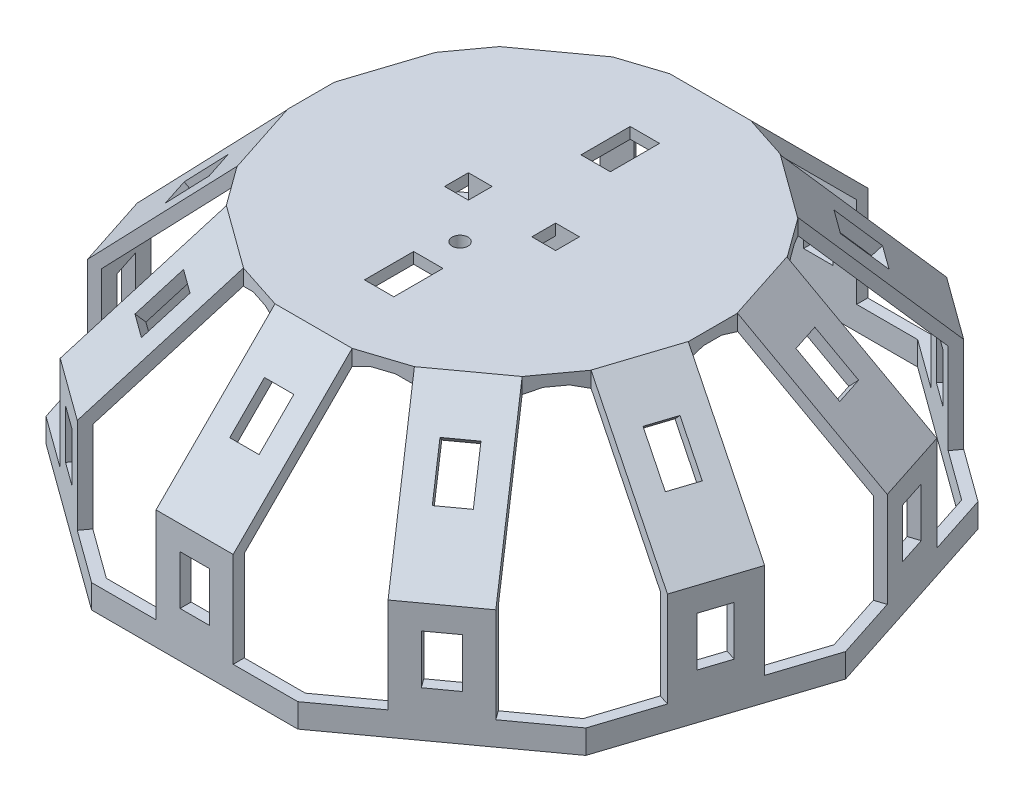
SolidWorks part; units mm, degrees
ref_plane "Front Plane" through (0, 0, 0) normal (0, 0, 1) x (1, 0, 0)
ref_plane "Top Plane" through (0, 0, 0) normal (0, 1, 0) x (1, 0, 0)
ref_plane "Right Plane" through (0, 0, 0) normal (1, 0, 0) x (0, 0, -1)
sketch "Sketch1" plane through (0, 0, 0) normal (0, 1, 0) x (1, 0, 0)
  line L0 (-34.026, -24.7214) -> (-12.9968, -40)
  line L1 (42.0585, 0) -> (34.026, 24.7214)
  line L2 (34.026, 24.7214) -> (12.9968, 40)
  line L3 (12.9968, 40) -> (-12.9968, 40)
  line L4 (-12.9968, 40) -> (-34.026, 24.7214)
  line L5 (-34.026, 24.7214) -> (-42.0585, 0)
  line L6 (-42.0585, 0) -> (-34.026, -24.7214)
  line L7 (-12.9968, -40) -> (12.9968, -40)
  line L8 (12.9968, -40) -> (34.026, -24.7214)
  line L9 (34.026, -24.7214) -> (42.0585, 0)
  circle A0 centre (0, 0) radius 40 construction
  point P14 (0, 40)
  dimension "D1" = 40
extrude "Boss-Extrude1" add sketch "Sketch1" along normal blind 30
chamfer "Chamfer1" distance 15 angle 45 10 edges at (23.5114, 30, 32.3607) (0, 30, 40) (-23.5114, 30, 32.3607) (-38.0423, 30, 12.3607) (-38.0423, 30, -12.3607) (-23.5114, 30, -32.3607) (0, 30, -40) (23.5114, 30, -32.3607) (38.0423, 30, -12.3607) (38.0423, 30, 12.3607)
ref_plane "Half Height Plane" through (0, 15, 0) normal (0, -1, 0) x (-1, 0, 0)
ref_plane "Sensor Reference Plane 1" through (0, 22.5, 0) normal (0, 1, 0) x (1, 0, 0)
ref_plane "Sensor Reference Plane 2" through (0, 7.5, 0) normal (0, -1, 0) x (-1, 0, 0)
ref_plane "Plane Angle 1" through (0, 0, 0) normal (-1, 0, 0) x (0, 0, 1)
ref_plane "Plane Angle 2" through (0, 0, 0) normal (0.809, 0, -0.5878) x (-0.5878, 0, -0.809)
ref_plane "Plane Angle 3" through (0, 0, 0) normal (0.309, 0, -0.9511) x (-0.9511, 0, -0.309)
ref_plane "Plane Angle 4" through (0, 0, 0) normal (-0.309, 0, -0.9511) x (-0.9511, 0, 0.309)
ref_plane "Plane Angle 5" through (0, 0, 0) normal (-0.809, 0, -0.5878) x (-0.5878, 0, 0.809)
sketch3d "3DSketch2"
  line L0 (-8.123, 30, 25) -> (8.123, 30, 25) construction
  line L1 (8.123, 30, -25) -> (-8.123, 30, -25) construction
  line L2 (0, 7.5, 40) -> (0, 7.5, 50)
  line L3 (38.0423, 7.5, 12.3607) -> (47.5528, 7.5, 15.4508)
  line L4 (0, 22.5, 32.5) -> (0, 29.5711, 39.5711)
  line L5 (23.5114, 7.5, 32.3607) -> (29.3893, 7.5, 40.4508)
  line L6 (19.103, 22.5, 26.2931) -> (23.2593, 29.5711, 32.0137)
  line L7 (30.9093, 22.5, 10.0431) -> (37.6343, 29.5711, 12.2281)
  line L8 (38.0423, 7.5, -12.3607) -> (47.5528, 7.5, -15.4508)
  line L9 (30.9093, 22.5, -10.0431) -> (37.6343, 29.5711, -12.2281)
  line L10 (23.5114, 7.5, -32.3607) -> (29.3893, 7.5, -40.4508)
  line L11 (19.103, 22.5, -26.2931) -> (23.2593, 29.5711, -32.0137)
  line L12 (0, 7.5, -40) -> (0, 7.5, -50)
  line L13 (0, 22.5, -32.5) -> (0, 29.5711, -39.5711)
  line L14 (-23.5114, 7.5, -32.3607) -> (-29.3893, 7.5, -40.4508)
  line L15 (-19.103, 22.5, -26.2931) -> (-23.2593, 29.5711, -32.0137)
  line L16 (-38.0423, 7.5, -12.3607) -> (-47.5528, 7.5, -15.4508)
  line L17 (-30.9093, 22.5, -10.0431) -> (-37.6343, 29.5711, -12.2281)
  line L18 (-38.0423, 7.5, 12.3607) -> (-47.5528, 7.5, 15.4508)
  line L19 (-30.9093, 22.5, 10.0431) -> (-37.6343, 29.5711, 12.2281)
  line L20 (-23.5114, 7.5, 32.3607) -> (-29.3893, 7.5, 40.4508)
  line L21 (-19.103, 22.5, 26.2931) -> (-23.2593, 29.5711, 32.0137)
  line L22 (0, 30, 15) -> (0, 40, 15)
  line L23 (0, 30, -15) -> (0, 40, -15)
  point P0 (0, 22.5, 32.5)
  point P1 (19.103, 22.5, 26.2931)
  point P2 (0, 7.5, 40)
  point P3 (23.5114, 7.5, 32.3607)
  point P4 (30.9093, 22.5, 10.0431)
  point P5 (38.0423, 7.5, 12.3607)
  point P6 (30.9093, 22.5, -10.0431)
  point P7 (38.0423, 7.5, -12.3607)
  point P8 (19.103, 22.5, -26.2931)
  point P9 (23.5114, 7.5, -32.3607)
  point P10 (0, 22.5, -32.5)
  point P11 (0, 7.5, -40)
  point P12 (-19.103, 22.5, -26.2931)
  point P13 (-23.5114, 7.5, -32.3607)
  point P14 (-38.0423, 7.5, -12.3607)
  point P16 (-30.9093, 22.5, 10.0431)
  point P17 (-38.0423, 7.5, 12.3607)
  point P18 (-23.5114, 7.5, 32.3607)
  point P19 (-19.103, 22.5, 26.2931)
  point P20 (0, 30, 15)
  point P21 (0, 30, -15)
  point P25 (-30.9093, 22.5, -10.0431)
  dimension "D1" = 10
  dimension "D2" = 10
  dimension "D3" = 10
shell "Shell1" thickness 1.4
sketch "Sketch6" plane through (0, 30, 0) normal (0, 1, 0) x (1, 0, 0)
  line L1 (1.85, -16.75) -> (-1.85, -16.75)
  line L2 (1.85, -16.75) -> (1.85, -10.55)
  line L3 (1.85, -10.55) -> (-1.85, -10.55)
  line L4 (-1.85, -16.75) -> (-1.85, -10.55)
  line L5 (1.85, 10.55) -> (-1.85, 10.55)
  line L6 (1.85, 10.55) -> (1.85, 16.75)
  line L7 (1.85, 16.75) -> (-1.85, 16.75)
  line L8 (-1.85, 10.55) -> (-1.85, 16.75)
  point P8 (0, -10.55)
  point P11 (0, 10.55)
  dimension "D3" = 1.75
  dimension "D1" = 6.2
  dimension "D2" = 3.7
  dimension "D4" = 1.75
extrude "Cut-Extrude6" cut sketch "Sketch6" against normal blind 10
sketch "Sketch4" plane through (0, 0, 40) normal (0, 0, 1) x (1, 0, 0)
  line L1 (1.85, 5.75) -> (-1.85, 5.75)
  line L2 (1.85, 5.75) -> (1.85, 11.95)
  line L3 (1.85, 11.95) -> (-1.85, 11.95)
  line L4 (-1.85, 5.75) -> (-1.85, 11.95)
  point P4 (0, 11.95)
  dimension "D1" = 3.7
  dimension "D2" = 6.2
  dimension "D3" = 1.75
extrude "Cut-Extrude4" cut sketch "Sketch4" against normal blind 10
sketch "Sketch5" plane through (0, 27.5, 27.5) normal (0, 0.7071, 0.7071) x (1, 0, 0)
  line L1 (-1.85, -2.6211) -> (1.85, -2.6211)
  line L2 (-1.85, -2.6211) -> (-1.85, -8.8211)
  line L3 (-1.85, -8.8211) -> (1.85, -8.8211)
  line L4 (1.85, -2.6211) -> (1.85, -8.8211)
  point P4 (0, -2.6211)
  dimension "D3" = 1.75
  dimension "D1" = 6.2
  dimension "D2" = 3.7
extrude "Cut-Extrude5" cut sketch "Sketch5" against normal blind 10
pattern_circular "CirPattern7" count 10 over 360 about axis through (0, 0, 0) along (0, 1, 0) of "Cut-Extrude4", "Cut-Extrude5"
sketch "Sketch8" plane through (0, 30, 0) normal (0, 1, 0) x (1, 0, 0)
  line L0 (10.7709, -23.0762) -> (19.5877, -35.2114)
  line L1 (8.123, -25) -> (21.2663, -15.4508) construction
  line L2 (34.026, -24.7214) -> (12.9968, -40) construction
  line L3 (19.5877, -35.2114) -> (12.9968, -40)
  line L4 (12.9968, -40) -> (4.85, -40)
  line L5 (12.9968, -40) -> (-12.9968, -40) construction
  line L6 (4.85, -40) -> (4.85, -25)
  line L7 (-8.123, -25) -> (8.123, -25) construction
  line L10 (1.85, -33.7374) -> (1.85, -29.3534) construction
  line L11 (15.7568, -24.8348) -> (18.3337, -28.3816) construction
  line L12 (4.85, -25) -> (10.7709, -23.0762)
  dimension "D1" = 3
  dimension "D2" = 3
extrude "Cut-Extrude8" cut sketch "Sketch8" against normal offset from surface (27 mm away) 3 up to face at (0, 0, 0)
pattern_circular "CirPattern9" count 10 over 360 about axis through (-0.0126, 0, -0.0387) along (0, 1, 0) of "Cut-Extrude8"
sketch "Sketch9" plane through (0, 30, 0) normal (0, 1, 0) x (1, 0, 0)
  line L0 (25.3033, 3.0263) -> (25.3033, -3.0263) construction
  line L1 (4, 1.5) -> (7, 1.5)
  line L2 (4, 1.5) -> (4, -1.5)
  line L3 (4, -1.5) -> (7, -1.5)
  line L4 (7, 1.5) -> (7, -1.5)
  line L5 (-7, 1.5) -> (-4, 1.5)
  line L6 (-7, 1.5) -> (-7, -1.5)
  line L7 (-7, -1.5) -> (-4, -1.5)
  line L8 (-4, 1.5) -> (-4, -1.5)
  line L9 (1.85, -10.55) -> (-1.85, -10.55) construction
  circle A0 centre (0, -6.55) radius 1
  point P10 (25.3033, 0)
  point P11 (4, 0)
  point P14 (0, -10.55)
  dimension "D5" = 2
  dimension "D1" = 3
  dimension "D2" = 3
  dimension "D3" = 4
  dimension "D4" = 4
  dimension "D6" = 4
extrude "Cut-Extrude9" cut sketch "Sketch9" against normal up to surface (1.4 mm away) up to face at (0, 28.6, 13.65)
sketch "Sketch10" plane through (0, 28.6, 0) normal (0, -1, 0) x (1, 0, 0)
  line L0 (-7, 1.5) -> (-7, -1.5) construction
  line L1 (7, 1.5) -> (-7, 1.5)
  line L2 (7, 1.5) -> (7, 3.5)
  line L3 (7, 3.5) -> (-7, 3.5)
  line L4 (-7, 1.5) -> (-7, 3.5)
  line L5 (7, -1.5) -> (7, 1.5) construction
  line L6 (-7, -1.5) -> (7, -1.5)
  line L7 (-7, -1.5) -> (-7, -3.5)
  line L8 (-7, -3.5) -> (7, -3.5)
  line L9 (7, -1.5) -> (7, -3.5)
  dimension "D1" = 2
  dimension "D2" = 2
extrude "Boss-Extrude2" add sketch "Sketch10" along normal blind 4
equation "\"Sensor Width\"= 3.5"
equation "\"Sensor Height\"= 6"
equation "\"Sensor Center to Top\"= 1.75"
equation "\"Umbrella Width\"= 80"
equation "\"Umbrella Height\"= 30"
equation "\"Compliance 1\"= 0.2"
equation "\"D1@Boss-Extrude1\"=\"Umbrella Height\""
equation "\"D1@Chamfer1\"=\"Umbrella Height\" / 2"
equation "\"D2@Sketch4\"=\"Sensor Height\" + \"Compliance 1\""
equation "\"D1@Sketch4\"=\"Sensor Width\" + \"Compliance 1\""
equation "\"D3@Sketch4\"=\"Sensor Center to Top\""
equation "\"D1@Sketch5\"=\"Sensor Height\" + \"Compliance 1\""
equation "\"D2@Sketch5\"=\"Sensor Width\" + \"Compliance 1\""
equation "\"D3@Sketch5\"=\"Sensor Center to Top\" "
equation "\"D1@Sketch6\"=\"Sensor Height\" + \"Compliance 1\""
equation "\"D2@Sketch6\"=\"Sensor Width\" + \"Compliance 1\""
equation "\"D3@Sketch6\"=\"Sensor Center to Top\""
equation "\"D4@Sketch6\"=\"Sensor Center to Top\""
equation "\"D1@Sketch1\"=\"Umbrella Width\" / 2"
